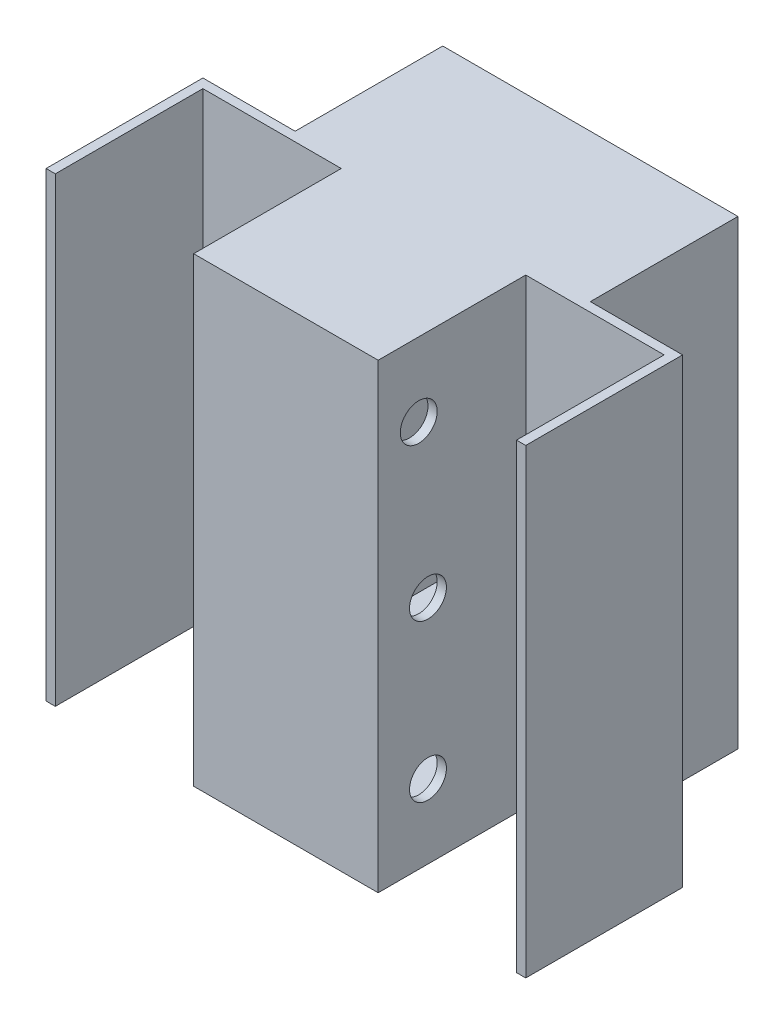
SolidWorks part; units mm, degrees
ref_plane "Plan de face" through (0, 0, 0) normal (0, 0, 1) x (1, 0, 0)
ref_plane "Plan de dessus" through (0, 0, 0) normal (0, 1, 0) x (1, 0, 0)
ref_plane "Plan de droite" through (0, 0, 0) normal (1, 0, 0) x (0, 0, -1)
sketch "Esquisse1" plane through (0, 0, 0) normal (0, 0, 1) x (1, 0, 0)
  line L1 (0, 0) -> (-45, 0)
  line L2 (0, 0) -> (0, 250)
  line L3 (0, 250) -> (-45, 250)
  line L4 (-45, 0) -> (-45, 250)
  dimension "D1" = 250
  dimension "D2" = 45
extrude "Boss.-Extru.1" add sketch "Esquisse1" along normal blind 5
sketch "Esquisse2" plane through (0, 0, 0) normal (1, 0, 0) x (0, 0, -1)
  line L1 (-5, 250) -> (75, 250)
  line L2 (-5, 250) -> (-5, 0)
  line L3 (-5, 0) -> (75, 0)
  line L4 (75, 250) -> (75, 0)
  dimension "D1" = 80
extrude "Boss.-Extru.2" add sketch "Esquisse2" along normal blind 5
sketch "Esquisse4" plane through (0, 0, -75) normal (0, 0, -1) x (-1, 0, 0)
  line L1 (0, 250) -> (-80, 250)
  line L2 (0, 250) -> (0, 0)
  line L3 (0, 0) -> (-80, 0)
  line L4 (-80, 250) -> (-80, 0)
  dimension "D1" = 250
  dimension "D2" = 80
extrude "Boss.-Extru.4" add sketch "Esquisse4" along normal blind 5
sketch "Esquisse5" plane through (80, 0, 0) normal (1, 0, 0) x (0, 0, -1)
  line L0 (-5, 250) -> (-5, 0) construction
  line L1 (80, 250) -> (-5, 250)
  line L2 (80, 250) -> (80, 0)
  line L3 (80, 0) -> (-5, 0)
  line L4 (-5, 250) -> (-5, 0)
  line L5 (-5, 0) -> (75, 0) construction
extrude "Boss.-Extru.5" add sketch "Esquisse5" along normal blind 5
sketch "Esquisse6" plane through (5, 0, 0) normal (1, 0, 0) x (0, 0, -1)
  line L2 (-5, 250) -> (-5, 0) construction
  line L3 (80, 250) -> (0, 250) construction
  line L4 (0, 0) -> (80, 0) construction
  circle A0 centre (22, 40) radius 35
  circle A1 centre (22, 125) radius 35
  circle A2 centre (17, 210) radius 35
  circle A3 centre (17, 210) radius 10
  circle A4 centre (22, 125) radius 10
  circle A5 centre (22, 40) radius 10
  dimension "D4" = 70
  dimension "D5" = 70
  dimension "D6" = 70
  dimension "D9" = 20
  dimension "D10" = 20
  dimension "D11" = 20
  dimension "D2" = 125
  dimension "D3" = 40
  dimension "D7" = 27
  dimension "D8" = 22
  dimension "D12" = 40
extrude "Enlèv. mat.-Extru.1" cut sketch "Esquisse6" against normal blind 5 contours A5 | A4 | A3
sketch "Esquisse7" plane through (0, 0, -80) normal (0, 0, -1) x (-1, 0, 0)
  line L0 (-85, 0) -> (-85, 250) construction
  line L1 (0, 250) -> (-85, 250) construction
  line L2 (-85, 0) -> (0, 0) construction
  circle A0 centre (-70, 235) radius 25
  circle A1 centre (-70, 15) radius 25
  circle A2 centre (-70, 235) radius 5
  circle A3 centre (-70, 15) radius 5
  dimension "D1" = 50
  dimension "D2" = 50
  dimension "D7" = 10
  dimension "D8" = 10
  dimension "D3" = 15
  dimension "D4" = 15
  dimension "D5" = 15
  dimension "D6" = 15
sketch "Esquisse8" plane through (0, 0, -80) normal (0, 0, -1) x (-1, 0, 0)
  line L1 (0, 250) -> (-85, 250) construction
  line L2 (-35, 250) -> (-30, 250)
  line L3 (-35, 250) -> (-35, 0)
  line L4 (-35, 0) -> (-30, 0)
  line L7 (-30, 250) -> (-30, 0)
  line L8 (-85, 0) -> (0, 0) construction
  line L9 (-85, 0) -> (-85, 250) construction
  dimension "D1" = 50
  dimension "D2" = 5
extrude "Boss.-Extru.6" add sketch "Esquisse8" along normal blind 80
sketch "Esquisse9" plane through (35, 0, 0) normal (1, 0, 0) x (0, 0, -1)
  line L0 (160, 250) -> (80, 250) construction
  line L1 (160, 125) -> (80, 125) construction
  line L2 (160, 250) -> (160, 0) construction
  line L3 (80, 250) -> (80, 0) construction
  line L4 (160, 0) -> (80, 0) construction
  circle A0 centre (110, 150) radius 20
  circle A1 centre (110, 100) radius 20
  circle A2 centre (110, 195) radius 20
  circle A3 centre (110, 55) radius 20
  dimension "D1" = 40
  dimension "D2" = 40
  dimension "D3" = 40
  dimension "D5" = 55
  dimension "D6" = 55
  dimension "D4" = 40
  dimension "D7" = 25
  dimension "D8" = 25
mirror "Symétrie2" about plane through (-45, 0, 5) normal (1, 0, 0) of "Boss.-Extru.2", "Boss.-Extru.4", "Enlèv. mat.-Extru.1", "Boss.-Extru.5", "Boss.-Extru.1", "Boss.-Extru.6"
sketch3d "Esquisse3D1"
  line L0 (30, 0, -160) -> (30, 0, -80)
  line L1 (30, 0, -80) -> (0, 0, -80)
  line L2 (0, 0, -80) -> (0, 0, 0)
  line L3 (0, 0, 0) -> (-90, 0, 0)
  line L4 (-90, 0, 0) -> (-90, 0, -80)
  line L5 (-90, 0, -80) -> (-120, 0, -80)
  line L6 (-120, 0, -80) -> (-120, 0, -160)
  line L7 (-120, 0, -160) -> (30, 0, -160)
extrude "Boss.-Extru.7" add sketch "Esquisse3D1" along a picked direction on the side against the normal blind 5
sketch3d "Esquisse3D2"
  line L0 (-120, 250, -160) -> (-120, 250, -80)
  line L1 (-120, 250, -80) -> (-90, 250, -80)
  line L2 (-90, 250, -80) -> (-90, 250, 0)
  line L3 (-90, 250, 0) -> (0, 250, 0)
  line L4 (0, 250, 0) -> (0, 250, -80)
  line L5 (0, 250, -80) -> (30, 250, -80)
  line L6 (30, 250, -80) -> (30, 250, -160)
  line L7 (30, 250, -160) -> (-120, 250, -160)
sketch3d "Esquisse3D3"
  line L0 (-120, 250, -160) -> (-120, 250, -80)
  line L1 (-120, 250, -80) -> (-90, 250, -80)
  line L2 (-90, 250, -80) -> (-90, 250, 0)
  line L3 (-90, 250, 0) -> (0, 250, 0)
  line L4 (0, 250, 0) -> (0, 250, -80)
  line L5 (0, 250, -80) -> (30, 250, -80)
  line L6 (30, 250, -80) -> (30, 250, -160)
  line L7 (30, 250, -160) -> (-120, 250, -160)
extrude "Boss.-Extru.9" add sketch "Esquisse3D3" along a picked direction on the side against the normal blind 5
sketch "Esquisse10" plane through (-125, 0, 0) normal (-1, 0, 0) x (0, 0, 1)
  circle A0 centre (-110, 195) radius 20
  circle A1 centre (-110, 100) radius 20
